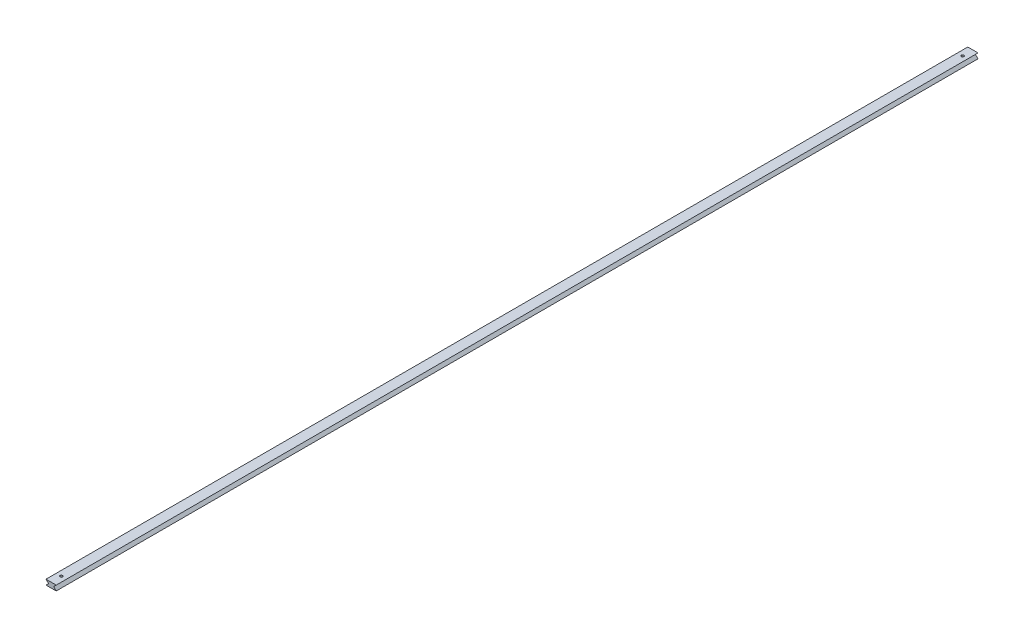
SolidWorks part; units mm, degrees
ref_plane "Ön Düzlem" through (0, 0, 0) normal (0, 0, 1) x (1, 0, 0)
ref_plane "Üst Düzlem" through (0, 0, 0) normal (0, 1, 0) x (1, 0, 0)
ref_plane "Sağ Düzlem" through (0, 0, 0) normal (1, 0, 0) x (0, 0, -1)
sketch "Çizim1" plane through (0, 0, 0) normal (0, 0, 1) x (1, 0, 0)
  line L0 (0, 0) -> (20, 0)
  line L1 (20, 0) -> (15, -5)
  line L2 (15, -5) -> (20, -10)
  line L3 (20, -10) -> (0, -10)
  line L4 (0, -10) -> (5, -5)
  line L5 (5, -5) -> (0, 0)
  dimension "D1" = 20
  dimension "D2" = 5
  dimension "D3" = 5
  dimension "D4" = 45
  dimension "D5" = 45
  dimension "D6" = 5
  dimension "D7" = 20
extrude "Yükseklik-Ekstrüzyon1" add sketch "Çizim1" along normal blind 1800
sketch "Çizim2" plane through (0, 0, 0) normal (0, 1, 0) x (1, 0, 0)
  line L0 (20, 0) -> (0, 0) construction
  line L1 (0, -1800) -> (0, 0) construction
  line L3 (20, -1800) -> (0, -1800) construction
  circle A0 centre (10, -20) radius 2.5
  circle A1 centre (10, -1780) radius 2.5
  dimension "D1" = 20
  dimension "D3" = 20
  dimension "D4" = 5
  dimension "D2" = 10
extrude "Kes-Ekstrüzyon5" cut sketch "Çizim2" against normal blind 10
